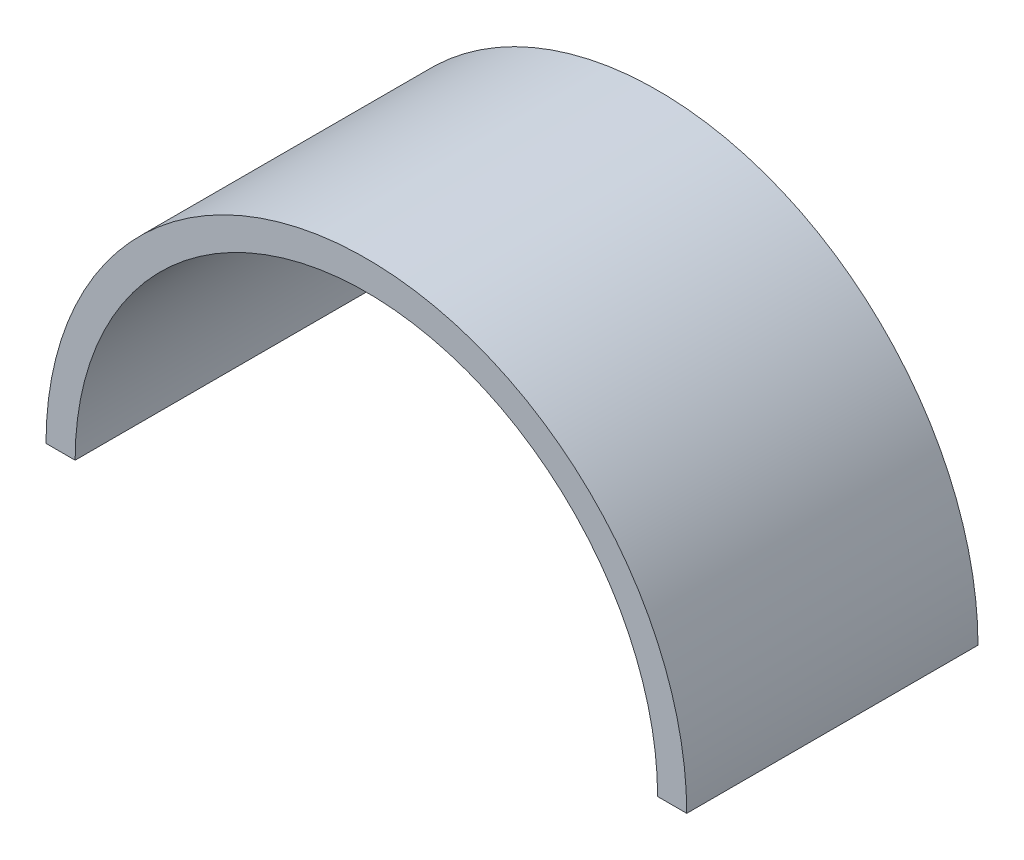
SolidWorks part; units mm, degrees
ref_plane "Front Plane" through (0, 0, 0) normal (0, 0, 1) x (1, 0, 0)
ref_plane "Top Plane" through (0, 0, 0) normal (0, 1, 0) x (1, 0, 0)
ref_plane "Right Plane" through (0, 0, 0) normal (1, 0, 0) x (0, 0, -1)
sketch "Sketch1" plane through (0, 0, 0) normal (0, 0, 1) x (1, 0, 0)
  line L0 (55, 0) -> (50, 0)
  line L1 (-50, 0) -> (-55, 0)
  arc A0 (55, 0) -> (-55, 0) centre (0, 0) ccw
  arc A1 (50, 0) -> (-50, 0) centre (0, 0) ccw
  dimension "D1" = 110
  dimension "D2" = 100
extrude "Boss-Extrude1" add sketch "Sketch1" along normal blind 50
sketch "Sketch2" plane through (0, 0, 0) normal (0, 0, -1) x (-1, 0, 0)
  line L0 (-55, 0) -> (55, 0) construction
  line L1 (0, 55) -> (0, 0) construction
  circle A0 centre (0, 0) radius 55 construction
  circle A1 centre (0, 52.5) radius 1.6
  arc A11 (55, 0) -> (-55, 0) centre (0, 0) ccw construction
  circle A12 centre (33.7463, 40.2173) radius 1.6
  circle A13 centre (51.7024, 9.1165) radius 1.6
  circle A14 centre (-51.7024, 9.1165) radius 1.6
  circle A15 centre (-33.7463, 40.2173) radius 1.6
  point P13 (0, 0)
  point P20 (0, 0)
  point P22 (0, 0)
  point P26 (0, 0)
  dimension "D1" = 3.2
  dimension "D2" = 52.5
  dimension "D3" = 3
extrude "Cut-Extrude1" cut sketch "Sketch2" against normal blind 10
